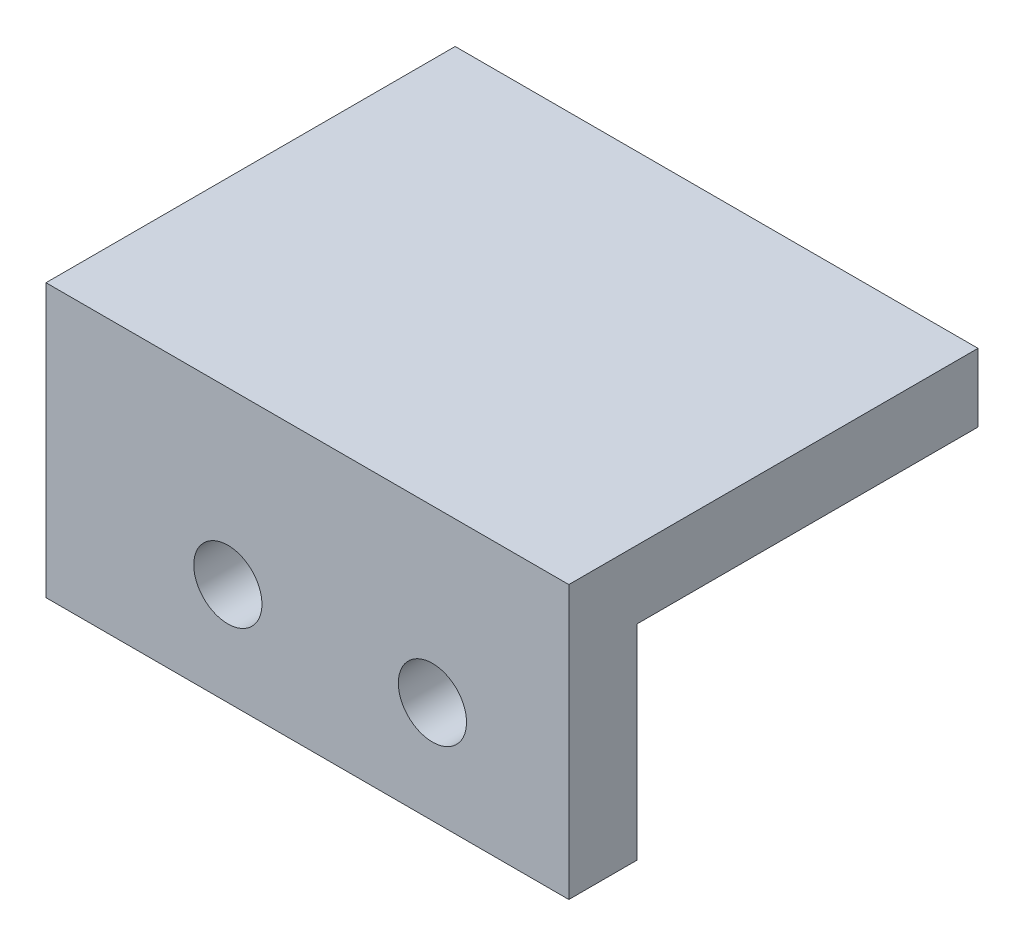
SolidWorks part; units mm, degrees
ref_plane "Alzado" through (0, 0, 0) normal (0, 0, 1) x (1, 0, 0)
ref_plane "Planta" through (0, 0, 0) normal (0, 1, 0) x (1, 0, 0)
ref_plane "Vista lateral" through (0, 0, 0) normal (1, 0, 0) x (0, 0, -1)
sketch "Croquis1" plane through (0, 0, 0) normal (0, 0, 1) x (1, 0, 0)
  line L1 (-11.5, -6) -> (11.5, -6)
  line L2 (-11.5, -6) -> (-11.5, 6)
  line L3 (-11.5, 6) -> (11.5, 6)
  line L4 (11.5, -6) -> (11.5, 6)
  line L5 (-11.5, -6) -> (11.5, 6) construction
  line L6 (-11.5, 6) -> (11.5, -6) construction
  point P0 (0, 0)
  dimension "D1" = 23
  dimension "D2" = 12
extrude "Saliente-Extruir1" add sketch "Croquis1" along normal blind 18
sketch "Croquis2" plane through (11.5, 0, 0) normal (1, 0, 0) x (0, 0, -1)
  line L0 (-18, -6) -> (-18, 6) construction
  line L1 (0, -6) -> (-15, -6)
  line L2 (0, -6) -> (0, 3)
  line L3 (0, 3) -> (-15, 3)
  line L4 (-15, -6) -> (-15, 3)
  line L5 (-18, 6) -> (0, 6) construction
  dimension "D1" = 3
  dimension "D2" = 3
extrude "Cortar-Extruir1" cut sketch "Croquis2" against normal blind 20
sketch "Croquis3" plane through (-11.5, 0, 0) normal (-1, 0, 0) x (0, 0, 1)
  line L0 (18, -6) -> (0, -6) construction
  line L1 (15, -6) -> (13.9, -6)
  line L2 (15, -6) -> (15, 3)
  line L3 (15, 3) -> (13.9, 3)
  line L4 (13.9, -6) -> (13.9, 3)
  line L5 (18, 6) -> (18, -6) construction
  line L6 (18, 6) -> (0, 6) construction
  dimension "D1" = 1.1
  dimension "D2" = 3
  dimension "D3" = 3
extrude "Cortar-Extruir2" cut sketch "Croquis3" against normal through all
sketch "Croquis4" plane through (0, 0, 15) normal (0, 0, -1) x (-1, 0, 0)
  circle A0 centre (-5.5, -1.5) radius 1.5
  circle A1 centre (3.5, -1.5) radius 1.5
  dimension "D1" = 3
extrude "Cortar-Extruir3" cut sketch "Croquis4" against normal through all
